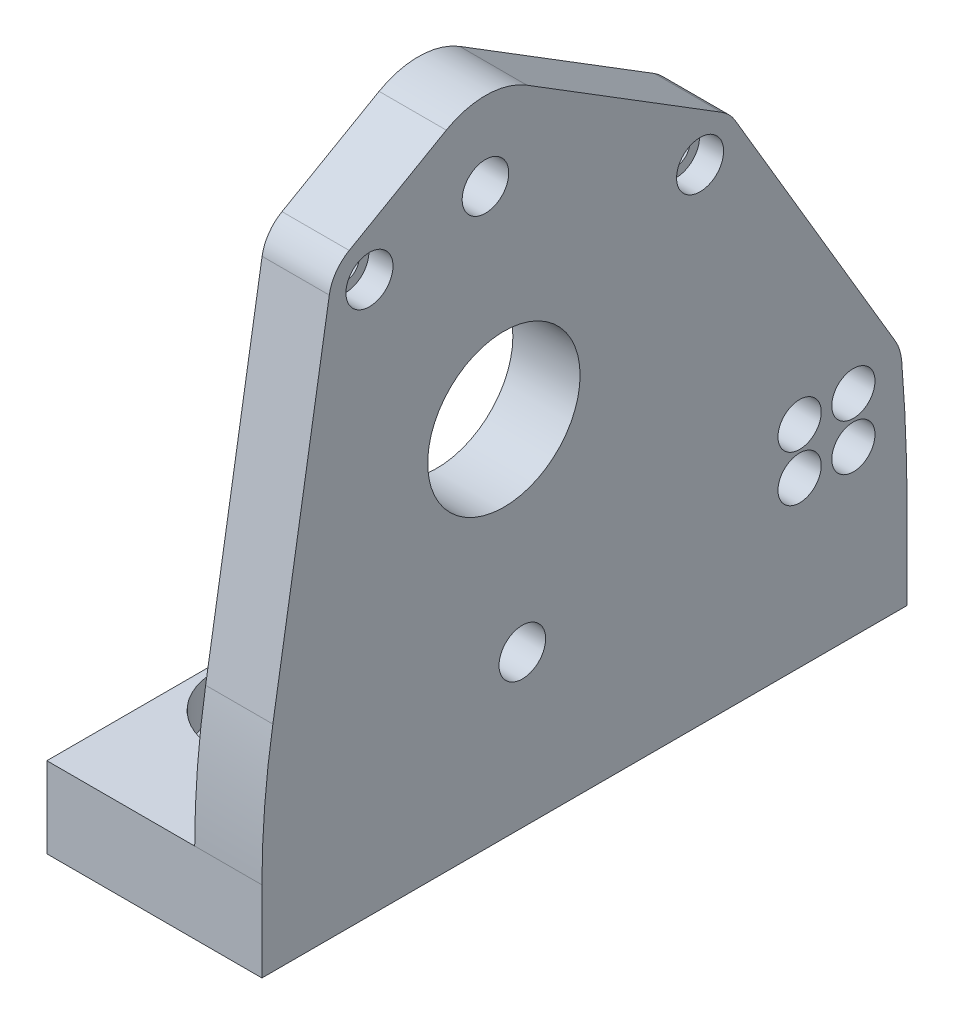
SolidWorks part; units mm, degrees
material "6061-T6 (SS)"
ref_plane "Front Plane" through (0, 0, 0) normal (0, 0, 1) x (1, 0, 0)
ref_plane "Top Plane" through (0, 0, 0) normal (0, 1, 0) x (1, 0, 0)
ref_plane "Right Plane" through (0, 0, 0) normal (1, 0, 0) x (0, 0, -1)
sketch "Sketch1" plane through (0, 0, 0) normal (0, 0, 1) x (1, 0, 0)
  line L0 (0, 0) -> (0, 9.525)
  line L1 (0, 9.525) -> (17.4625, 9.525)
  line L2 (17.4625, 9.525) -> (17.4625, 79.375)
  line L3 (17.4625, 79.375) -> (25.4, 79.375)
  line L4 (25.4, 79.375) -> (25.4, 0)
  line L5 (25.4, 0) -> (0, 0)
  dimension "D1" = 17.4625
  dimension "D2" = 7.9375
  dimension "D3" = 79.375
  dimension "D4" = 9.525
extrude "Boss-Extrude1" add sketch "Sketch1" along normal blind 76.2
sketch "Sketch2" plane through (0, 0, 0) normal (1, 0, 0) x (0, 0, -1)
  line L0 (-76.2, 79.375) -> (-76.2, 9.525) construction
  line L1 (-47.625, 42.8625) -> (-49.8039, 67.7674) construction
  line L2 (-76.2, 9.525) -> (0, 9.525) construction
  line L3 (-76.2, 9.525) -> (0, 9.525) construction
  line L4 (-47.625, 42.8625) -> (-45.4461, 17.9576) construction
  line L5 (-47.625, 42.8625) -> (-38.625, 42.8625) construction
  line L6 (-34.925, 42.8625) -> (-60.325, 42.8625) construction
  line L7 (-60.325, 42.8625) -> (-60.325, 79.375) construction
  line L8 (-34.925, 42.8625) -> (-34.925, 79.375) construction
  line L9 (-76.2, 79.375) -> (0, 79.375) construction
  line L10 (-35.8917, 38.0024) -> (-59.3583, 47.7226) construction
  line L11 (-59.3583, 47.7226) -> (-46.2474, 79.375) construction
  line L12 (-35.8917, 38.0024) -> (-18.7546, 79.375) construction
  line L13 (-35.8917, 38.0024) -> (-27.3866, 58.5356)
  line L14 (-60.325, 42.8625) -> (-60.325, 65.0875)
  line L15 (-24.4533, 57.3206) -> (-27.3866, 58.5356) construction
  line L16 (-6.35, 24.8635) -> (0, 24.8635) construction
  line L17 (0, 79.375) -> (0, 9.525) construction
  line L18 (-12.7, 24.8635) -> (-6.35, 24.8635) construction
  line L19 (-47.625, 42.8625) -> (-57.3452, 19.396) construction
  line L20 (-57.3452, 19.396) -> (-70.5451, 24.8635) construction
  line L21 (-6.35, 19.396) -> (-12.7, 19.396) construction
  circle A0 centre (-47.625, 42.8625) radius 9 construction
  circle A1 centre (-63.5, 65.0875) radius 3.175
  circle A3 centre (-24.4533, 57.3206) radius 3.175
  point P5 (-47.625, 42.8625)
  point P12 (-76.2, 9.525)
  point P22 (-47.625, 42.8625)
  point P25 (-12.7, 24.8635)
  point P32 (-6.35, 24.8635)
  point P42 (0, 0)
  point P43 (0, 0)
  dimension "D1" = 18
  dimension "D9" = 6.35
  dimension "D2" = 50
  dimension "D3" = 33.3375
  dimension "D4" = 28.575
  dimension "D5" = 85
  dimension "D6" = 25.4
  dimension "D7" = 22.5
  dimension "D8" = 22.225
  dimension "D10" = 6.35
  dimension "D12" = 14.2875
  dimension "D11" = 25.4
hole_wizard "Ø18.0mm Diameter Hole1" positions "Sketch7" profile "Sketch9" hole size "Ø1.0" standard "ANSI Metric" end condition through all
sketch "Sketch7" plane through (25.4, 0, 0) normal (1, 0, 0) x (0, 0, -1)
  point P0 (-47.625, 42.8625)
sketch "Sketch9" plane through (25.4, 42.8625, 47.625) normal (0, 1, 0) x (0, 0, -1)
  line L0 (0, 0) -> (0, 25.4)
  line L1 (0, 25.4) -> (9, 25.4)
  line L2 (9, 25.4) -> (9, 0)
  line L5 (9, 0) -> (0, 0)
  line L11 (0, -6.35) -> (0, 107.95) construction
  dimension "Thru Hole Dia." = 18
  dimension "Thru Hole Depth" = 25.4
hole_wizard "CBORE for M5 Hex Head Bolt1" positions "Sketch3" profile "Sketch4" counterbore size "M5" standard "ANSI Metric"
sketch "Sketch3" plane through (17.4625, 0, 0) normal (-1, 0, 0) x (0, 0, 1)
  point P0 (49.8039, 67.7674)
  point P3 (45.4461, 17.9576)
sketch "Sketch4" plane through (17.4625, 67.7674, 49.8039) normal (0, 1, 0) x (0, 0, 1)
  line L0 (0, 0) -> (0, 47.6264)
  line L1 (0, 47.6264) -> (2.75, 45.974)
  line L2 (2.75, 45.974) -> (2.75, 3.58)
  line L3 (2.75, 3.58) -> (6.12, 3.58)
  line L4 (6.12, 3.58) -> (6.12, 0)
  line L5 (6.12, 0) -> (0, 0)
  line L10 (0, 47.6264) -> (-2.75, 45.974) construction
  line L11 (0, -6.35) -> (0, 107.95) construction
  dimension "Hole Dia." = 5.5
  dimension "Hole Depth" = 45.974
  dimension "C'Bore Dia." = 12.24
  dimension "C'Bore Depth" = 3.58
  dimension "Drill Angle" = 118
hole_wizard "CBORE for #4 Socket Head Cap Screw1" positions "Sketch5" profile "Sketch6" counterbore size "#4" standard "ANSI Inch"
sketch "Sketch5" plane through (25.4, 0, 0) normal (1, 0, 0) x (0, 0, -1)
  point P0 (-24.4533, 57.3206)
  point P3 (-63.5, 65.0875)
sketch "Sketch6" plane through (25.4, 57.3206, 24.4533) normal (0, 1, 0) x (0, 0, -1)
  line L0 (0, 0) -> (0, 46.9546)
  line L1 (0, 46.9546) -> (1.6319, 45.974)
  line L2 (1.6319, 45.974) -> (1.6319, 2.8448)
  line L3 (1.6319, 2.8448) -> (2.7788, 2.8448)
  line L4 (2.7788, 2.8448) -> (2.7788, 0)
  line L5 (2.7788, 0) -> (0, 0)
  line L10 (0, 46.9546) -> (-1.632, 45.974) construction
  line L11 (0, -6.35) -> (0, 107.95) construction
  dimension "Hole Dia." = 3.2639
  dimension "Hole Depth" = 45.974
  dimension "C'Bore Dia." = 5.5575
  dimension "C'Bore Depth" = 2.8448
  dimension "Drill Angle" = 118
hole_wizard "#10 Clearance Hole1" positions "Sketch11" profile "Sketch12" hole size "#10" standard "ANSI Inch" end condition through all
sketch "Sketch11" plane through (17.4625, 0, 0) normal (-1, 0, 0) x (0, 0, 1)
  point P0 (6.35, 24.8635)
  point P3 (12.7, 24.8635)
  point P6 (6.35, 19.396)
  point P9 (12.7, 19.396)
sketch "Sketch12" plane through (17.4625, 24.8635, 6.35) normal (0, 1, 0) x (0, 0, 1)
  line L0 (0, 0) -> (0, 7.9375)
  line L1 (0, 7.9375) -> (2.5527, 7.9375)
  line L2 (2.5527, 7.9375) -> (2.5527, 0)
  line L5 (2.5527, 0) -> (0, 0)
  line L11 (0, -6.35) -> (0, 107.95) construction
  dimension "Thru Hole Dia." = 5.1054
  dimension "Thru Hole Depth" = 7.9375
sketch "Sketch10" plane through (0, 0, 0) normal (1, 0, 0) x (0, 0, -1)
  line L0 (0, 9.525) -> (0, 79.375)
  line L1 (-76.2, 79.375) -> (0, 79.375)
  line L2 (-76.2, 79.375) -> (-76.2, 9.525)
  line L3 (-63.5, 65.0875) -> (-63.5, 66.7194) construction
  line L4 (-63.5, 66.7194) -> (-63.5, 69.8944) construction
  line L5 (-49.8039, 67.7674) -> (-49.8039, 73.8874) construction
  line L6 (-49.8039, 73.8874) -> (-49.8039, 77.0624) construction
  line L7 (-24.4533, 57.3206) -> (-24.4533, 58.9526) construction
  line L8 (-24.4533, 58.9526) -> (-24.4533, 62.1276) construction
  line L9 (-6.35, 24.8635) -> (-6.35, 27.4162) construction
  line L10 (-6.35, 27.4162) -> (-6.35, 30.5912) construction
  line L11 (-54.4275, 75.8308) -> (-65.8911, 69.2576)
  line L12 (-21.919, 61.4053) -> (-44.9035, 75.6657)
  line L13 (-20.3145, 59.7654) -> (-1.4184, 27.7767)
  line L14 (-68.2433, 65.8675) -> (-74.9094, 25.3275)
  arc A0 (-68.2433, 65.8675) -> (-65.8911, 69.2576) centre (-63.5, 65.0875) cw
  arc A1 (-54.4275, 75.8308) -> (-44.9035, 75.6657) centre (-49.8039, 67.7674) cw
  arc A2 (-21.919, 61.4053) -> (-20.3145, 59.7654) centre (-24.4533, 57.3206) cw
  arc A3 (-1.4184, 27.7767) -> (-0.6411, 25.3275) centre (-6.35, 24.8635) cw
  circle A4 centre (-63.5, 65.0875) radius 1.6319 construction
  circle A5 centre (-49.8039, 67.7674) radius 6.12 construction
  circle A6 centre (-24.4533, 57.3206) radius 1.6319 construction
  circle A7 centre (-6.35, 24.8635) radius 2.5527 construction
  arc A8 (0, 9.525) -> (-0.6411, 25.3275) centre (-195.0724, 9.525) ccw
  arc A9 (-74.9094, 25.3275) -> (-76.2, 9.525) centre (21.1928, 9.525) ccw
  dimension "D1" = 3.175
extrude "Cut-Extrude2" cut sketch "Sketch10" against normal through all and the other way through all contours A9 L14 A0 L11 A1 L12 A2 L13 A3 A8 L0 L1 L2
sketch "Sketch13" plane through (0, 0, 0) normal (0, 1, 0) x (1, 0, 0)
  line L0 (8.7312, 0) -> (8.7312, -38.1) construction
  line L1 (0, 0) -> (17.4625, 0) construction
  line L2 (0, 0) -> (0, -76.2) construction
  line L3 (0, -76.2) -> (17.4625, -76.2) construction
  line L4 (17.4625, 0) -> (17.4625, -76.2) construction
  line L5 (8.7312, -38.1) -> (8.7312, -76.2) construction
  line L6 (0, -38.1) -> (8.7312, -38.1) construction
  line L7 (8.7312, -38.1) -> (17.4625, -38.1) construction
  point P11 (8.7312, -57.15)
  point P12 (13.0969, -57.15)
  point P13 (13.0969, -38.1)
  point P16 (4.3656, -57.15)
  point P18 (4.3656, -38.1)
  point P20 (4.3656, -19.05)
  point P21 (8.7312, -19.05)
  point P22 (13.0969, -19.05)
hole_wizard "CBORE for 1/4 Hex Machine Screw1" positions "Sketch14" profile "Sketch15" counterbore size "1/4" standard "ANSI Inch" end condition through all
sketch "Sketch14" plane through (0, 9.525, 0) normal (0, 1, 0) x (1, 0, 0)
  point P3 (8.7312, -19.05)
  point P6 (8.7312, -57.15)
sketch "Sketch15" plane through (8.7312, 9.525, 19.05) normal (1, 0, 0) x (0, 0, 1)
  line L0 (0, 0) -> (0, 9.525)
  line L1 (0, 9.525) -> (3.3782, 9.525)
  line L3 (3.3782, 9.525) -> (3.3782, 4.826)
  line L4 (3.3782, 4.826) -> (7.9375, 4.826)
  line L5 (7.9375, 4.826) -> (7.9375, 0)
  line L7 (7.9375, 0) -> (0, 0)
  line L11 (0, -6.35) -> (0, 107.95) construction
  dimension "Thru Hole Dia." = 6.7564
  dimension "Thru Hole Depth" = 9.525
  dimension "C'Bore Dia." = 15.875
  dimension "C'Bore Depth" = 4.826
equation "\"D1@Sketch1\"=(1.5-1/8)/2"
equation "\"accelerator pedal length\"= 1in"
equation "\"accelerator pedal travel angle\"= 22.5deg"
equation "\"accelerator pedal end stop diameter\"= 0.25in"
equation "\"potentiometer mounting holes c2c\"= 50mm"
equation "\"potentiometer shaft diameter\"= 14mm"
equation "\"D1@Sketch2\"=\"potentiometer shaft diameter\"+4mm"
equation "\"D2@Sketch2\"=\"potentiometer mounting holes c2c\""
equation "\"D6@Sketch2\"=\"accelerator pedal length\""
equation "\"D7@Sketch2\"=\"accelerator pedal travel angle\""
equation "\"D9@Sketch2\"=\"accelerator pedal end stop diameter\""
equation "\"D5@Sketch2\"=85"
